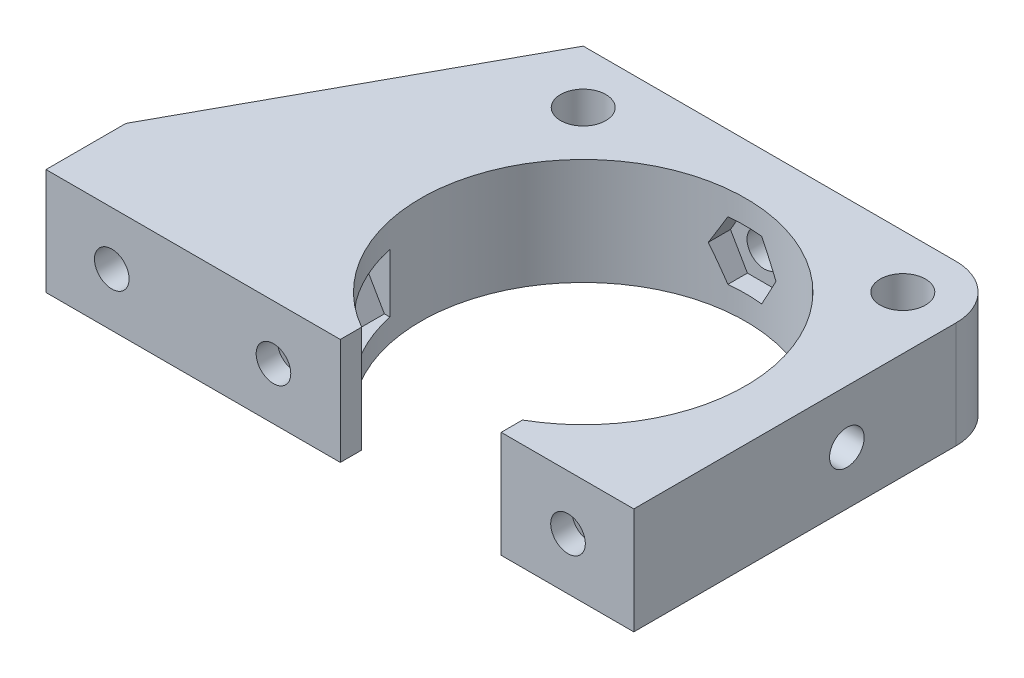
SolidWorks part; units mm, degrees
ref_plane "Alzado" through (0, 0, 0) normal (0, 0, 1) x (1, 0, 0)
ref_plane "Planta" through (0, 0, 0) normal (0, 1, 0) x (1, 0, 0)
ref_plane "Vista lateral" through (0, 0, 0) normal (1, 0, 0) x (0, 0, -1)
sketch "Croquis1" plane through (0, 0, 0) normal (0, 1, 0) x (1, 0, 0)
  line L0 (0, 20) -> (0, -20) construction
  line L1 (-20, 20) -> (20, 20)
  line L2 (-20, 20) -> (-20, -20)
  line L3 (-20, -20) -> (20, -20)
  line L4 (20, 20) -> (20, -20)
  line L5 (-20, 20) -> (20, -20) construction
  line L6 (-20, -20) -> (20, 20) construction
  line L7 (-20, -4.25) -> (-30, -7.25)
  line L8 (-30, -7.25) -> (-30, -15.25)
  line L9 (-30, -15.25) -> (30, -15.25)
  line L10 (20, -4.25) -> (30, -7.25)
  line L11 (30, -7.25) -> (30, -15.25)
  circle A0 centre (-15, 15) radius 2.125
  circle A1 centre (15, 15) radius 2.125
  circle A4 centre (0, 0) radius 15.25
  circle A5 centre (-15, -15) radius 2.125 [skipped]
  circle A6 centre (15, -15) radius 2.125 [skipped]
  point P0 (0, 0)
  point P25 (0, -15.25)
  dimension "D3" = 4.25
  dimension "D7" = 30.5
  dimension "D1" = 40
  dimension "D2" = 40
  dimension "D4" = 5
  dimension "D5" = 2
  dimension "D8" = 8
  dimension "D9" = 10
  dimension "D10" = 15.25
  dimension "D12" = 3
  dimension "D6" = 2
extrude "Soporte caja reductora" add sketch "Croquis1" against normal blind 20
sketch "Croquis3" plane through (0, 0, 15.25) normal (0, 0, 1) x (1, 0, 0)
  line L3 (-20, -20) -> (-20, 0) construction
  circle A0 centre (-23.5, -10) radius 2.125
  circle A1 centre (23.5, -10) radius 2.125
  dimension "D1" = 4.25
  dimension "D2" = 3.5
extrude "Cortar-Extruir1" cut sketch "Croquis3" against normal through all
fillet "Redondeo1" radius 5 2 edges at (-20, -10, -20) (20, -10, -20)
sketch "Sketch1" plane through (0, 0, 0) normal (0, 1, 0) x (1, 0, 0)
  line L0 (15, 20) -> (30, 20)
  line L1 (30, 20) -> (30, 8)
  line L2 (30, 8) -> (25.5, 8)
  line L4 (25.5, 8) -> (25.5, 15)
  line L5 (25.5, 15) -> (20, 15)
  circle A0 centre (15, 15) radius 5
  arc M37 (20, 15) -> (15, 20) centre (15, 15) ccw
  dimension "D1" = 12
  dimension "D2" = 5.5
extrude "Boss-Extrude1" add sketch "Sketch1" along direction (0, 1, 0) on the side against the normal up to surface (20 mm away) contours L5 L4 L2 L1 L0 M37
sketch "Sketch2" plane through (0, 0, -20) normal (0, 0, -1) x (-1, 0, 0)
  line L1 (-20, -20) -> (-20, 0) construction
  circle A0 centre (-22.75, -10) radius 1.625
  dimension "D1" = 3.25
  dimension "D2" = 2.75
extrude "Cut-Extrude1" cut sketch "Sketch2" against normal up to next
sketch "Sketch3" plane through (0, 0, -15) normal (0, 0, 1) x (1, 0, 0)
  line L1 (20, -11.5877) -> (22.75, -13.1754)
  line L2 (22.75, -13.1754) -> (25.5, -11.5877)
  line L3 (25.5, -11.5877) -> (25.5, -8.4123)
  line L4 (25.5, -8.4123) -> (22.75, -6.8246)
  line L5 (22.75, -6.8246) -> (20, -8.4123)
  line L6 (20, -8.4123) -> (20, -11.5877)
  circle A0 centre (22.75, -10) radius 2.75 construction
  dimension "D1" = 5.5
extrude "Cut-Extrude2" cut sketch "Sketch3" against normal blind 2
sketch "Sketch4" plane through (25.5, 0, 0) normal (-1, 0, 0) x (0, 0, 1)
  line L5 (-15, -8.4123) -> (-15, 0) construction
  line L6 (-20, 0) -> (-8, 0) construction
  circle A0 centre (-12.25, -10) radius 1.625
  dimension "D1" = 2.75
  dimension "D2" = 3.25
  dimension "D3" = 10
extrude "Cut-Extrude3" cut sketch "Sketch4" against normal through all
sketch "Sketch5" plane through (30, 0, 0) normal (1, 0, 0) x (0, 0, -1)
  line L1 (15, -11.5877) -> (15, -8.4123)
  line L2 (15, -8.4123) -> (12.25, -6.8246)
  line L3 (12.25, -6.8246) -> (9.5, -8.4123)
  line L4 (9.5, -8.4123) -> (9.5, -11.5877)
  line L5 (9.5, -11.5877) -> (12.25, -13.1754)
  line L6 (12.25, -13.1754) -> (15, -11.5877)
  circle A0 centre (12.25, -10) radius 2.75 construction
  dimension "D1" = 5.5
extrude "Cut-Extrude4" cut sketch "Sketch5" along normal blind 2 from surface
sketch "Croquis6" plane through (0, 0, 0) normal (0, 1, 0) x (1, 0, 0)
  line L0 (-20, -20) -> (20, -20) construction
  line L1 (-15.25, 0) -> (15.25, 0)
  line L2 (-15.25, 0) -> (-15.25, -20)
  line L3 (-15.25, -20) -> (15.25, -20)
  line L4 (15.25, 0) -> (15.25, -20)
  line L6 (-20, -20) -> (20, -20)
  line L7 (-20, -20) -> (-20, -15.25)
  line L8 (-20, -15.25) -> (20, -15.25)
  line L9 (20, -20) -> (20, -15.25)
  circle A0 centre (0, 0) radius 15.25 construction
  circle M5 centre (0, 0) radius 15.25
  line M14 (-20, -15.25) -> (-20, -20)
  line M15 (-20, -20) -> (20, -20)
  line M16 (20, -20) -> (20, -15.25)
extrude "Cortar-Extruir17" cut sketch "Croquis6" against normal through all contours L8 L2 L4 M15 | L8 L2 M14 M15 | L2 L8 M5 | L8 L4 M5 | L8 L4 M15 M16
mirror "Simetría1" about plane through (0, 0, 0) normal (0, 1, 0) of bodies 111
sketch "Croquis7" plane through (0, 0, -20) normal (0, 0, -1) x (-1, 0, 0)
  line L1 (-30, 0) -> (30, 0)
  line L2 (-30, 0) -> (-30, -20)
  line L3 (-30, -20) -> (30, -20)
  line L4 (30, 0) -> (30, -20)
extrude "Cortar-Extruir18" cut sketch "Croquis7" against normal through all
sketch "Croquis8" plane through (0, 20, 0) normal (0, 1, 0) x (1, 0, 0)
  line L3 (-15, 20) -> (30, 20) construction
  line L4 (-11.0405, 13.9391) -> (-10.3152, 11.2321)
  line L5 (10.8174, 13.8793) -> (10.3152, 11.2321)
  line L59 (10.8174, 13.8793) -> (11.9787, 20)
  line L60 (-11.0405, 13.9391) -> (-12.6645, 20)
  line L61 (11.9787, 20) -> (-12.6645, 20)
  circle A0 centre (0, 0) radius 15.25
extrude "Saliente-Extruir2" add sketch "Croquis8" along normal blind 49
sketch "Croquis9" plane through (0, 69, 0) normal (0, 1, 0) x (1, 0, 0)
  line L0 (-20, 0) -> (20, 0)
  line L1 (-20, 15) -> (-20, -4.25) construction
  line L2 (20, 15) -> (20, -4.25) construction
  line L3 (-20, 0) -> (-20, 15)
  line L4 (-15, 20) -> (12.6645, 20)
  line L5 (12.6645, 20) -> (20, 13.9368)
  line L6 (20, 13.9368) -> (20, 0)
  line L7 (20, 0) -> (20.1759, -0.147)
  line L8 (-14.75, 0) -> (-14.75, -15.25)
  line L9 (-15.25, -15.25) -> (-30, -15.25)
  line L10 (-30, -15.25) -> (-30, -7.25)
  line L11 (-30, -7.25) -> (-20, -4.25)
  line L12 (-20, -4.25) -> (-20, 0)
  line L13 (-14.75, -15.25) -> (-15.25, -15.25)
  line L14 (-14.75, -15.25) -> (0, -15.25)
  line L15 (0, -15.25) -> (0, -14.75)
  circle A0 centre (0, 0) radius 14.75
  circle A1 centre (-15, 15) radius 5
  dimension "D1" = 29.5
extrude "Soporte motor" add sketch "Croquis9" against normal blind 15 from offset 15 offset against normal yes
sketch "Croquis12" plane through (0, 0, 15.25) normal (0, 0, 1) x (1, 0, 0)
  line L1 (0, 54) -> (-30, 54) construction
  line L2 (-20, 39) -> (-20, 54) construction
  circle A0 centre (-23.5, 46.5) radius 2.125
  dimension "D3" = 4.25
  dimension "D1" = 7.5
  dimension "D2" = 3.5
extrude "Agujeros de sujecion a base" cut sketch "Croquis12" against normal through all
sketch "Croquis13" plane through (0, 0, 15.25) normal (0, 0, 1) x (1, 0, 0)
  line L1 (-20, 44.4793) -> (-20, 48.5207)
  line L2 (-20, 48.5207) -> (-23.5, 50.5415)
  line L3 (-23.5, 50.5415) -> (-27, 48.5207)
  line L4 (-27, 48.5207) -> (-27, 44.4793)
  line L5 (-27, 44.4793) -> (-23.5, 42.4585)
  line L6 (-23.5, 42.4585) -> (-20, 44.4793)
  circle A0 centre (-23.5, 46.5) radius 3.5 construction
  dimension "D1" = 7
extrude "Tuerca Agujero de sujecion a base" cut sketch "Croquis13" against normal blind 10 from offset 4 offset against normal yes
sketch "Croquis10" plane through (0, 69, 0) normal (0, 1, 0) x (1, 0, 0)
  line L0 (-10.3152, 11.2321) -> (-9.8079, 9.3388)
  line L1 (10.3152, 11.2321) -> (9.4813, 8.1201)
  circle A0 centre (0, 0) radius 14.75
  circle A1 centre (0, 0) radius 15.25
  arc M2 (-10.3152, 11.2321) -> (10.3152, 11.2321) centre (0, 0) cw
extrude "Saliente-Extruir4" add sketch "Croquis10" against normal up to surface (15 mm away) contours A0 L1 L0 M2
sketch "Croquis11" plane through (0, 0, 0) normal (0, -1, 0) x (1, 0, 0)
  line L0 (0, 0) -> (0, -12.6937) construction
  line L1 (15, -20) -> (30, -20)
  line L2 (30, -20) -> (30, 15.25)
  line L3 (30, 15.25) -> (15.25, 15.25)
  line L4 (15.25, 0) -> (15.25, 15.25) construction
  line L5 (15.25, 15.25) -> (30, 15.25) construction
  line L6 (15.25, 15.25) -> (15.25, 4.25)
  line L7 (15.25, 4.25) -> (20, 4.25)
  line L8 (20, 4.25) -> (20, -15)
  circle A0 centre (0, 0) radius 22.5
  circle A1 centre (-15, -15) radius 5
  circle A2 centre (15, -15) radius 5
  line M8 (-15, -20) -> (30, -20)
  line M9 (30, -20) -> (30, -8)
  line M10 (30, -8) -> (25.5, -8)
  line M11 (25.5, -8) -> (25.5, -15)
  line M12 (25.5, -15) -> (20, -15)
  line M14 (20, 4.25) -> (30, 7.25)
  line M15 (30, 7.25) -> (30, 15.25)
  line M16 (30, 15.25) -> (15.25, 15.25)
  line M17 (15.25, 15.25) -> (15.25, 0)
  dimension "D1" = 45
extrude "Cortar-Extruir19" cut sketch "Croquis11" against normal blind 25 contours A0 L3 L7 M14 M17 | A0 M14 M15 M16 | A2 M12 M8 M9 M10 M11
mirror "Simetría2"
sketch "Croquis14" plane through (0, 0, 15.25) normal (0, 0, 1) x (1, 0, 0)
  line L1 (-30, 20) -> (20, 20)
  line L2 (-30, 20) -> (-30, 138)
  line L3 (-30, 138) -> (20, 138)
  line L4 (20, 20) -> (20, 138)
extrude "Cortar-Extruir22" cut sketch "Croquis14" against normal through all
sketch "Croquis15" plane through (0, 0, 0) normal (0, -1, 0) x (1, 0, 0)
  line L0 (-30, 7.25) -> (-30, 15.25) construction
  line L1 (-20, 4.25) -> (-30, 4.25)
  line L2 (-20, 4.25) -> (-20, 11.25)
  line L3 (-20, 11.25) -> (-30, 11.25)
  line L4 (-30, 4.25) -> (-30, 11.25)
  line L5 (-30, 15.25) -> (-15.25, 15.25) construction
  dimension "D1" = 4
extrude "Cortar-Extruir23" cut sketch "Croquis15" against normal through all
sketch "Croquis16" plane through (0, 0, 0) normal (0, -1, 0) x (1, 0, 0)
  line L0 (-15.25, 0) -> (-15.25, 15.25) construction
  line L1 (-30, 15.25) -> (-15.25, 15.25)
  line L2 (-30, 15.25) -> (-30, 12.75)
  line L3 (-20, 12.75) -> (-15.25, 12.75)
  line L4 (-15.25, 15.25) -> (-15.25, 12.75)
  line L5 (-30, 12.75) -> (-30, 11.25)
  line L6 (-30, 11.25) -> (-20, 11.25)
  line L7 (-20, 11.25) -> (-30, 11.25) construction
  line L8 (-20, -15) -> (-20, 11.25) construction
  line L9 (-20, 11.25) -> (-20, 12.75)
  dimension "D1" = 2.5
extrude "Cortar-Extruir24" cut sketch "Croquis16" against normal through all
sketch "Croquis18" plane through (0, 0, -20) normal (0, 0, -1) x (-1, 0, 0)
  line L0 (20, 0) -> (20, 20) construction
  line L1 (-20, 0) -> (20, 0)
  line L2 (-20, 0) -> (-20, 10)
  line L3 (-20, 10) -> (20, 10)
  line L4 (20, 0) -> (20, 10)
  line L5 (15, 20) -> (-15, 20) construction
  dimension "D1" = 10
extrude "Cortar-Extruir25" cut sketch "Croquis18" against normal through all
sketch "Croquis19" plane through (0, 20, 0) normal (0, 1, 0) x (1, 0, 0)
  line L0 (-20, -12.75) -> (-34, -12.75)
  line L1 (-34, -12.75) -> (-34, -7.75)
  line L2 (-34, -7.75) -> (-24, -7.75)
  line L3 (-24, -7.75) -> (-20, -3.75)
  line L4 (-20, 15) -> (-20, -12.75) construction
  line L5 (-20, -3.75) -> (-20, -12.75)
  dimension "D1" = 5
  dimension "D2" = 4
  dimension "D3" = 4
  dimension "D4" = 10
extrude "Saliente-Extruir5" add sketch "Croquis19" against normal up to surface (10 mm away) up to face at (15, 10, -12.875)
sketch "Croquis20" plane through (0, 0, 7.75) normal (0, 0, -1) x (-1, 0, 0)
  circle A0 centre (29, 15) radius 1
  dimension "D1" = 2
extrude "Cortar-Extruir26" cut sketch "Croquis20" against normal through all
sketch "Croquis21" plane through (20, 0, 0) normal (1, 0, 0) x (0, 0, -1)
  line L1 (20, 20) -> (20, 10) construction
  circle A0 centre (4.75, 15) radius 1.625
  dimension "D1" = 3.25
  dimension "D2" = 15.25
extrude "Cortar-Extruir27" cut sketch "Croquis21" against normal up to next
sketch "Croquis22" plane through (0, 10, 0) normal (0, -1, 0) x (1, 0, 0)
  circle A0 centre (-15, -15) radius 2.125
  circle A1 centre (15, -15) radius 2.125
  circle A2 centre (15, -15) radius 1
  circle A3 centre (-15, -15) radius 1
  dimension "D1" = 2
extrude "Saliente-Extruir6" add sketch "Croquis22" against normal blind 10
sketch "Croquis23" plane through (0, 0, -20) normal (0, 0, -1) x (-1, 0, 0)
  circle A0 centre (0, 15) radius 1.625
  dimension "D1" = 3.25
extrude "Cortar-Extruir28" cut sketch "Croquis23" against normal through all
sketch "Croquis24" plane through (0, 0, -20) normal (0, 0, -1) x (-1, 0, 0)
  line L1 (1.5877, 12.25) -> (3.1754, 15)
  line L2 (3.1754, 15) -> (1.5877, 17.75)
  line L3 (1.5877, 17.75) -> (-1.5877, 17.75)
  line L4 (-1.5877, 17.75) -> (-3.1754, 15)
  line L5 (-3.1754, 15) -> (-1.5877, 12.25)
  line L6 (-1.5877, 12.25) -> (1.5877, 12.25)
  circle A0 centre (0, 15) radius 2.75 construction
  dimension "D1" = 5.5
extrude "Cortar-Extruir29" cut sketch "Croquis24" against normal blind 10 from offset 3 offset against normal yes
sketch "Croquis26" plane through (0, 10, 0) normal (0, -1, 0) x (1, 0, 0)
  line L0 (-29, 12.75) -> (-58.825, 12.75)
  line L1 (-58.825, 12.75) -> (-39.1605, -4.1045)
  line L3 (-39.5945, 1.5357) -> (-46.8449, 7.75)
  line L4 (-46.8449, 7.75) -> (-34.2682, 7.75)
  line L5 (-34.2682, 7.75) -> (-39.5945, 1.5357)
  line L7 (-29, 7.75) -> (-35.7321, -0.1045)
  line L8 (-29, 7.75) -> (-29, 12.75)
  line L9 (-34, 7.75) -> (-24, 7.75) construction
  line L10 (-34, 12.75) -> (-15.25, 12.75) construction
  line L11 (-39.1605, -4.1045) -> (-20, -4.1045)
  line L12 (-20, 3.75) -> (-20, -15) construction
  line L13 (-20, -4.1045) -> (-20, -0.1045)
  line L14 (-20, -0.1045) -> (-35.7321, -0.1045)
  dimension "D1" = 4
  dimension "D2" = 4
  dimension "D3" = 4
  dimension "D4" = 29.825
  dimension "D5" = 40.6
extrude "Saliente-Extruir7" add sketch "Croquis26" against normal blind 10
sketch "Croquis27" plane through (0, 0, 12.75) normal (0, 0, 1) x (1, 0, 0)
  line L0 (-29, 16) -> (-29, 14) construction
  line L1 (-46.8449, 20) -> (-46.8449, 10) construction
  circle A0 centre (-40.5449, 15) radius 1.625
  circle A2 centre (-29, 15) radius 1.625
  dimension "D1" = 3.25
  dimension "D2" = 6.3
extrude "Cortar-Extruir30" cut sketch "Croquis27" against normal up to next
sketch "Croquis28" plane through (0, 0, 12.75) normal (0, 0, 1) x (1, 0, 0)
  line L1 (-38.9572, 12.25) -> (-37.3694, 15)
  line L2 (-37.3694, 15) -> (-38.9572, 17.75)
  line L3 (-38.9572, 17.75) -> (-42.1326, 17.75)
  line L4 (-42.1326, 17.75) -> (-43.7203, 15)
  line L5 (-43.7203, 15) -> (-42.1326, 12.25)
  line L6 (-42.1326, 12.25) -> (-38.9572, 12.25)
  line L7 (-27.4123, 12.25) -> (-25.8246, 15)
  line L8 (-25.8246, 15) -> (-27.4123, 17.75)
  line L9 (-27.4123, 17.75) -> (-30.5877, 17.75)
  line L10 (-30.5877, 17.75) -> (-32.1754, 15)
  line L11 (-32.1754, 15) -> (-30.5877, 12.25)
  line L12 (-30.5877, 12.25) -> (-27.4123, 12.25)
  circle A0 centre (-40.5449, 15) radius 2.75 construction
  circle A1 centre (-29, 15) radius 2.75 construction
  dimension "D1" = 5.5
extrude "Cortar-Extruir31" cut sketch "Croquis28" against normal up to next from offset 3 offset against normal yes
sketch "Croquis29" plane through (-18.6128, 0, -21.716) normal (-0.6508, 0, -0.7593) x (-0.7593, 0, 0.6508)
  line L2 (31.0624, 20) -> (31.0624, 10) construction
  circle A0 centre (33.8124, 15) radius 1.625
  dimension "D2" = 3.25
  dimension "D1" = 2.75
extrude "Cortar-Extruir32" cut sketch "Croquis29" against normal up to next
sketch "Croquis31" plane through (-18.6128, 0, -21.716) normal (-0.6508, 0, -0.7593) x (-0.7593, 0, 0.6508)
  line L1 (36.5624, 16.5877) -> (33.8124, 18.1754)
  line L2 (33.8124, 18.1754) -> (31.0624, 16.5877)
  line L3 (31.0624, 16.5877) -> (31.0624, 13.4123)
  line L4 (31.0624, 13.4123) -> (33.8124, 11.8246)
  line L5 (33.8124, 11.8246) -> (36.5624, 13.4123)
  line L6 (36.5624, 13.4123) -> (36.5624, 16.5877)
  circle A0 centre (33.8124, 15) radius 2.75 construction
  dimension "D1" = 5.5
extrude "Cortar-Extruir33" cut sketch "Croquis31" against normal up to next from offset 2.5 offset against normal yes
sketch "Croquis35" plane through (0, 20, 0) normal (0, 1, 0) x (1, 0, 0)
  line L0 (-15, 20) -> (15, 20) construction
  line L1 (10.3896, 0) -> (23.695, 0)
  line L2 (10.3896, 0) -> (10.3896, -6.8269)
  line L3 (10.3896, -6.8269) -> (23.695, -6.8269)
  line L4 (23.695, 0) -> (23.695, -6.8269)
  dimension "D1" = 20
extrude "Cortar-Extruir34" cut sketch "Croquis35" against normal through all both and the other way through all
sketch "Croquis36" plane through (20, 0, 0) normal (1, 0, 0) x (0, 0, -1)
  line L1 (7.5, 16.5877) -> (4.75, 18.1754)
  line L2 (4.75, 18.1754) -> (2, 16.5877)
  line L3 (2, 16.5877) -> (2, 13.4123)
  line L4 (2, 13.4123) -> (4.75, 11.8246)
  line L5 (4.75, 11.8246) -> (7.5, 13.4123)
  line L6 (7.5, 13.4123) -> (7.5, 16.5877)
  circle A0 centre (4.75, 15) radius 2.75 construction
  dimension "D1" = 5.5
extrude "Cortar-Extruir35" cut sketch "Croquis36" against normal blind 10 from offset 3 offset against normal yes
sketch "Croquis37" plane through (0, 10, 0) normal (0, -1, 0) x (1, 0, 0)
  line L0 (-39.1605, -4.1045) -> (-20.6149, -20)
  line L1 (-20.6149, -20) -> (-15, -20)
  line L2 (-33.014, -4.1045) -> (-19.5581, -15.6376)
  line L3 (-39.1605, -4.1045) -> (-20, -4.1045) construction
  line L4 (-19.5581, -15.6376) -> (-15, -20)
  line L5 (-58.825, 12.75) -> (-39.1605, -4.1045) construction
  line L6 (-39.5945, 1.5357) -> (-46.8449, 7.75) construction
  line L7 (-39.1605, -4.1045) -> (-33.014, -4.1045)
extrude "Saliente-Extruir8" add sketch "Croquis37" against normal blind 10
sketch "Croquis38" plane through (0, 10, 0) normal (0, -1, 0) x (1, 0, 0)
  line L0 (-58.825, 12.75) -> (-38.825, 12.75)
  line L1 (-58.825, 12.75) -> (-15.25, 12.75) construction
  line L2 (-38.825, 12.75) -> (-38.825, 9.75)
  line L3 (-38.825, 9.75) -> (-55.3248, 9.75)
  line L4 (-58.825, 12.75) -> (-20.6149, -20) construction
  line L5 (-55.3248, 9.75) -> (-58.825, 12.75)
  dimension "D1" = 3
  dimension "D2" = 20
extrude "Saliente-Extruir9" add sketch "Croquis38" along normal blind 13
sketch "Croquis39" plane through (0, 10, 0) normal (0, -1, 0) x (1, 0, 0)
  line L0 (-38.825, 9.75) -> (-38.825, 7.75)
  line L1 (-46.8449, 7.75) -> (-34.2682, 7.75) construction
  line L3 (-55.3248, 9.75) -> (-20.6149, -20) construction
  line L4 (-52.9914, 7.75) -> (-55.3248, 9.75)
  line L5 (-55.3248, 9.75) -> (-38.825, 9.75)
  line L6 (-52.9914, 7.75) -> (-50.658, 5.75)
  line L7 (-50.658, 5.75) -> (-38.825, 5.75)
  line L8 (-38.825, 5.75) -> (-38.825, 7.75)
  dimension "D1" = 2
extrude "Saliente-Extruir10" add sketch "Croquis39" along normal blind 3
mirror "Simetría3" of bodies 142
sketch "Croquis40" plane through (0, 0, -20) normal (0, 0, -1) x (-1, 0, 0)
  line L1 (-30.8963, 20) -> (75.6873, 20)
  line L2 (-30.8963, 20) -> (-30.8963, -27.3915)
  line L3 (-30.8963, -27.3915) -> (75.6873, -27.3915)
  line L4 (75.6873, 20) -> (75.6873, -27.3915)
extrude "Cortar-Extruir36" cut sketch "Croquis40" against normal through all both and the other way through all
sketch "Croquis41" plane through (0, 20, 0) normal (0, -1, 0) x (1, 0, 0)
  line L0 (-19.993, -22.3025) -> (-20, 3.75)
  line L1 (-20, 3.75) -> (-24, 7.75)
  line L2 (-24, 7.75) -> (-56.0351, 7.75)
  line L3 (-56.0351, 7.75) -> (-19.993, -22.3025)
extrude "Cortar-Extruir37" cut sketch "Croquis41" against normal through all both and the other way through all
sketch "Croquis42" plane through (0, 0, 9.75) normal (0, 0, -1) x (-1, 0, 0)
  line L0 (46.7203, 20) -> (46.7203, 30)
  line L1 (52.9914, 20) -> (24, 20) construction
  line L2 (46.7203, 30) -> (38.825, 30)
  line L3 (38.825, 30) -> (33.493, 43.7606)
  line L4 (33.493, 43.7606) -> (49.5253, 48.9514)
  line L5 (49.5253, 48.9514) -> (67.2004, 42.5122)
  line L6 (67.2004, 42.5122) -> (65.9066, 20)
  line L7 (65.9066, 20) -> (51.714, 13.8642)
  line L8 (51.714, 13.8642) -> (46.7203, 20)
  dimension "D1" = 3
extrude "Cortar-Extruir38" cut sketch "Croquis42" against normal through all both and the other way through all
sketch "Croquis43" plane through (0, 20, 0) normal (0, -1, 0) x (1, 0, 0)
  line L0 (-19.9936, -20) -> (-46.7203, 7.75)
  line L1 (-19.9936, -20) -> (-17.1126, -17.2252)
  line L2 (-46.7203, 7.75) -> (-43.8393, 10.5248)
  line L3 (-17.1126, -17.2252) -> (-43.8393, 10.5248)
  dimension "D1" = 4
extrude "Saliente-Extruir11" add sketch "Croquis43" against normal up to vertex (10 mm away)
sketch "Croquis44" plane through (0, 0, 9.75) normal (0, 0, -1) x (-1, 0, 0)
  line L7 (38.9572, 27.75) -> (37.3694, 25)
  line L8 (37.3694, 25) -> (38.9572, 22.25)
  line L9 (38.9572, 22.25) -> (42.1326, 22.25)
  line L10 (42.1326, 22.25) -> (43.7203, 25)
  line L11 (43.7203, 25) -> (42.1326, 27.75)
  line L12 (42.1326, 27.75) -> (38.9572, 27.75)
  circle A1 centre (40.5449, 25) radius 2.75 construction
extrude "Cortar-Extruir39" cut sketch "Croquis44" along normal through all
sketch "Croquis45" plane through (0, 0, 12.75) normal (0, 0, 1) x (1, 0, 0)
  line L1 (-46.7203, 30) -> (-15.25, 30)
  line L2 (-46.7203, 30) -> (-46.7203, 20)
  line L3 (-46.7203, 20) -> (-15.25, 20)
  line L4 (-15.25, 30) -> (-15.25, 20)
  circle A0 centre (-40.5449, 25) radius 1.625
  circle A1 centre (-29, 25) radius 1.625
extrude "Saliente-Extruir12" add sketch "Croquis45" along normal blind 2.5
sketch "Croquis46" plane through (0, 20, 0) normal (0, -1, 0) x (1, 0, 0)
  line L0 (15.25, 0) -> (20, 0)
  line L1 (20, 0) -> (20, 15.25)
  line L2 (-46.7203, 15.25) -> (-15.25, 15.25) construction
  line L3 (20, 15.25) -> (7.5498, 15.25)
  line L4 (7.5498, 15.25) -> (7.5498, 13.25)
  line L5 (-15.25, 0) -> (-15.25, 15.25)
  line L6 (-15.25, 15.25) -> (-7.5498, 15.25)
  line L7 (-7.5498, 15.25) -> (-7.5498, 13.25)
  arc A0 (-7.5498, 13.25) -> (-15.25, 0) centre (0, 0) ccw
  arc A1 (15.25, 0) -> (7.5498, 13.25) centre (0, 0) ccw
  dimension "D1" = 2
extrude "Saliente-Extruir13" add sketch "Croquis46" against normal up to vertex (10 mm away)
sketch "Croquis47" plane through (0, 0, 15.25) normal (0, 0, 1) x (1, 0, 0)
  line L1 (15.4123, 22.3525) -> (17, 25.1025)
  line L2 (17, 25.1025) -> (15.4123, 27.8525)
  line L3 (15.4123, 27.8525) -> (12.2369, 27.8525)
  line L4 (12.2369, 27.8525) -> (10.6491, 25.1025)
  line L5 (10.6491, 25.1025) -> (12.2369, 22.3525)
  line L6 (12.2369, 22.3525) -> (15.4123, 22.3525)
  line L10 (20, 30) -> (20, 20) construction
  line L11 (0, 20) -> (0, 0) construction
  line L12 (-15.25, 20) -> (15.25, 20) construction
  line L13 (-12.2369, 22.3525) -> (-15.4123, 22.3525)
  line L14 (-10.6491, 25.1025) -> (-12.2369, 22.3525)
  line L15 (-12.2369, 27.8525) -> (-10.6491, 25.1025)
  line L16 (-15.4123, 27.8525) -> (-12.2369, 27.8525)
  line L17 (-17, 25.1025) -> (-15.4123, 27.8525)
  line L18 (-15.4123, 22.3525) -> (-17, 25.1025)
  circle A0 centre (13.8246, 25.1025) radius 2.75 construction
  circle A1 centre (13.8246, 25.1025) radius 1.625
  circle A2 centre (-13.8246, 25.1025) radius 2.75 construction
  circle A3 centre (-13.8246, 25.1025) radius 1.625
  dimension "D1" = 3.25
  dimension "D2" = 5.5
  dimension "D3" = 3
extrude "Cortar-Extruir40" cut sketch "Croquis47" against normal blind 10 from offset 2 offset against normal yes
sketch "Croquis48" plane through (0, 0, 15.25) normal (0, 0, 1) x (1, 0, 0)
  circle A0 centre (13.8246, 25.1025) radius 1.625
  circle A1 centre (-13.8246, 25.1025) radius 1.625
extrude "Cortar-Extruir41" cut sketch "Croquis48" against normal up to vertex
sketch "Croquis49" plane through (0, 30, 0) normal (0, 1, 0) x (1, 0, 0)
  line L1 (-12.9793, 11.5) -> (-10.9585, 15)
  line L2 (-10.9585, 15) -> (-12.9793, 18.5)
  line L3 (-12.9793, 18.5) -> (-17.0207, 18.5)
  line L4 (-17.0207, 18.5) -> (-19.0415, 15)
  line L5 (-19.0415, 15) -> (-17.0207, 11.5)
  line L6 (-17.0207, 11.5) -> (-12.9793, 11.5)
  line L7 (17.0207, 11.5) -> (19.0415, 15)
  line L8 (19.0415, 15) -> (17.0207, 18.5)
  line L9 (17.0207, 18.5) -> (12.9793, 18.5)
  line L10 (12.9793, 18.5) -> (10.9585, 15)
  line L11 (10.9585, 15) -> (12.9793, 11.5)
  line L12 (12.9793, 11.5) -> (17.0207, 11.5)
  circle A0 centre (-15, 15) radius 3.5 construction
  circle A1 centre (15, 15) radius 3.5 construction
  dimension "D1" = 7
extrude "Cortar-Extruir42" cut sketch "Croquis49" against normal blind 3
mirror "Simetría4" about plane through (30.8963, 20, 12.75) normal (0, 1, 0) of bodies 153
sketch "Croquis50" plane through (0, 0, -20) normal (0, 0, -1) x (-1, 0, 0)
  line L1 (-27.9391, 20) -> (52.4763, 20)
  line L2 (-27.9391, 20) -> (-27.9391, 36.1457)
  line L3 (-27.9391, 36.1457) -> (52.4763, 36.1457)
  line L4 (52.4763, 20) -> (52.4763, 36.1457)
extrude "Cortar-Extruir43" cut sketch "Croquis50" against normal through all both and the other way through all
sketch "Croquis51" plane through (0, 10, 0) normal (0, -1, 0) x (1, 0, 0)
  circle A0 centre (-15, -15) radius 2.125
  circle A1 centre (15, -15) radius 2.125
  dimension "D1" = 4.25
extrude "Cortar-Extruir44" cut sketch "Croquis51" against normal through all both and the other way through all
sketch "Croquis52" plane through (0, 10, 0) normal (0, -1, 0) x (1, 0, 0)
  line L0 (-35.1754, 15.25) -> (-35.1754, 7.75)
  line L1 (-7.5498, 15.25) -> (-46.7203, 15.25) construction
  line L2 (-41.1668, 7.75) -> (-24, 7.75) construction
  line L3 (-35.1754, 7.75) -> (-19.9952, -14.2322)
  line L4 (-19.9952, -14.2322) -> (-19.9936, -20)
  line L5 (-19.9936, -20) -> (-54.5429, 5.516)
  line L6 (-54.5429, 5.516) -> (-50.4556, 20.9491)
  line L7 (-50.4556, 20.9491) -> (-35.1754, 15.25)
  dimension "D1" = 3
extrude "Cortar-Extruir45" cut sketch "Croquis52" against normal through all both and the other way through all
sketch "Croquis53" plane through (0, 10, 0) normal (0, -1, 0) x (1, 0, 0)
  line L0 (-35.1754, 7.75) -> (-19.9936, -20)
  line L1 (-19.9936, -20) -> (-20, 3.75)
  line L2 (-20, 3.75) -> (-24, 7.75)
  line L3 (-24, 7.75) -> (-35.1754, 7.75)
extrude "Saliente-Extruir14" add sketch "Croquis53" against normal blind 10
sketch "Croquis54" plane through (0, 0, 15.25) normal (0, 0, 1) x (1, 0, 0)
  line L1 (-27.4123, 17.75) -> (-30.5877, 17.75)
  line L2 (-30.5877, 17.75) -> (-32.1754, 15)
  line L3 (-32.1754, 15) -> (-30.5877, 12.25)
  line L4 (-30.5877, 12.25) -> (-27.4123, 12.25)
  line L5 (-27.4123, 12.25) -> (-25.8246, 15)
  line L6 (-25.8246, 15) -> (-27.4123, 17.75)
  circle A0 centre (-29, 15) radius 2.75 construction
extrude "Cortar-Extruir46" cut sketch "Croquis54" against normal through all from vertex at -5.5 starting at point (-27.4123, 17.75, 9.75)
